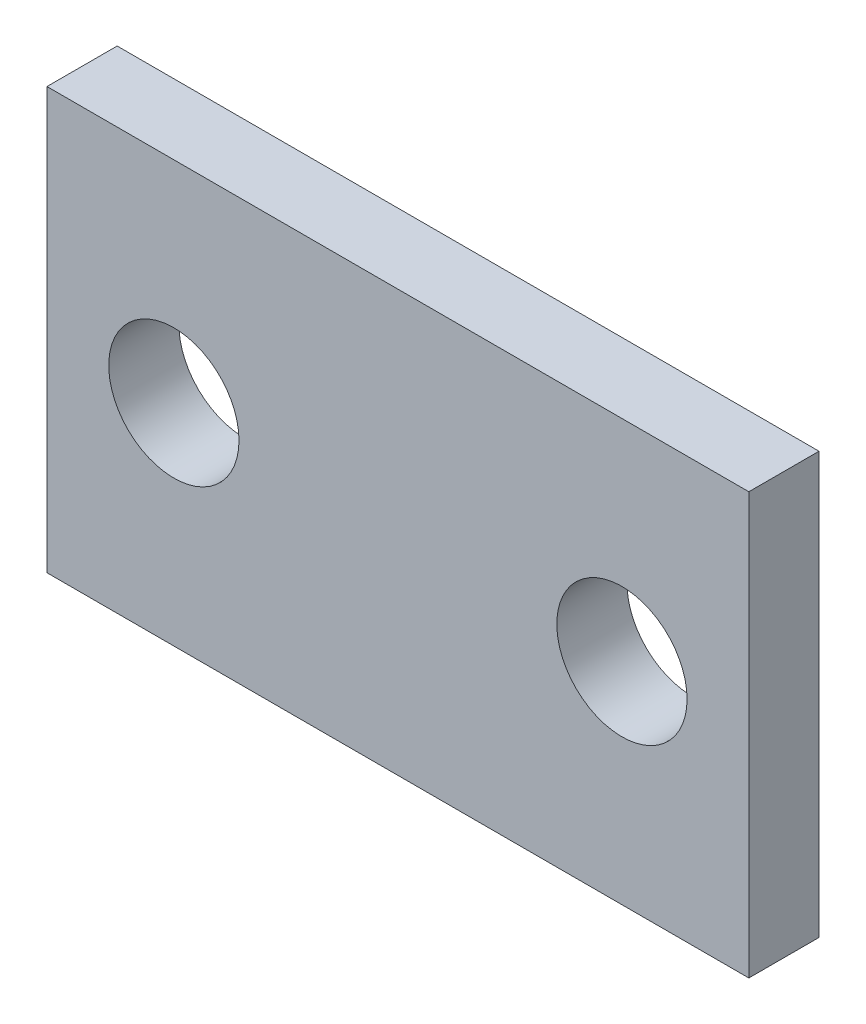
SolidWorks part; units mm, degrees
ref_plane "Front Plane" through (0, 0, 0) normal (0, 0, 1) x (1, 0, 0)
ref_plane "Top Plane" through (0, 0, 0) normal (0, 1, 0) x (1, 0, 0)
ref_plane "Right Plane" through (0, 0, 0) normal (1, 0, 0) x (0, 0, -1)
sketch "Sketch1" plane through (0, 0, 0) normal (0, 0, 1) x (1, 0, 0)
  line L1 (-7.9375, 4.7625) -> (7.9375, 4.7625)
  line L2 (-7.9375, 4.7625) -> (-7.9375, -4.7625)
  line L3 (-7.9375, -4.7625) -> (7.9375, -4.7625)
  line L4 (7.9375, 4.7625) -> (7.9375, -4.7625)
  line L5 (-7.9375, 4.7625) -> (7.9375, -4.7625) construction
  line L6 (-7.9375, -4.7625) -> (7.9375, 4.7625) construction
  point P0 (0, 0)
  dimension "D1" = 15.875
  dimension "D2" = 9.525
extrude "Boss-Extrude1" add sketch "Sketch1" along normal blind 1.5875
hole_wizard "#4 Clearance Hole1" positions "Sketch3" profile "Sketch2" hole size "#4" standard "Ansi Inch" end condition up to next
sketch "Sketch3" plane through (0, 0, 1.5875) normal (0, 0, 1) x (1, 0, 0)
  line L0 (7.9375, -4.7625) -> (7.9375, 4.7625) construction
  line L1 (-5.0673, 0) -> (5.0673, 0) construction
  point P0 (-5.0673, 0)
  point P1 (5.0673, 0)
  point P6 (7.9375, 0)
  dimension "D1" = 10.1346
sketch "Sketch2" plane through (-5.0673, 0, 1.5875) normal (1, 0, 0) x (0, -1, 0)
  line L0 (0, 0) -> (0, 1.5875)
  line L1 (0, 1.5875) -> (1.4732, 1.5875)
  line L2 (1.4732, 1.5875) -> (1.4732, 0)
  line L5 (1.4732, 0) -> (0, 0)
  line L11 (0, -6.35) -> (0, 107.95) construction
  dimension "Thru Hole Dia." = 2.9464
  dimension "Thru Hole Depth" = 1.5875
